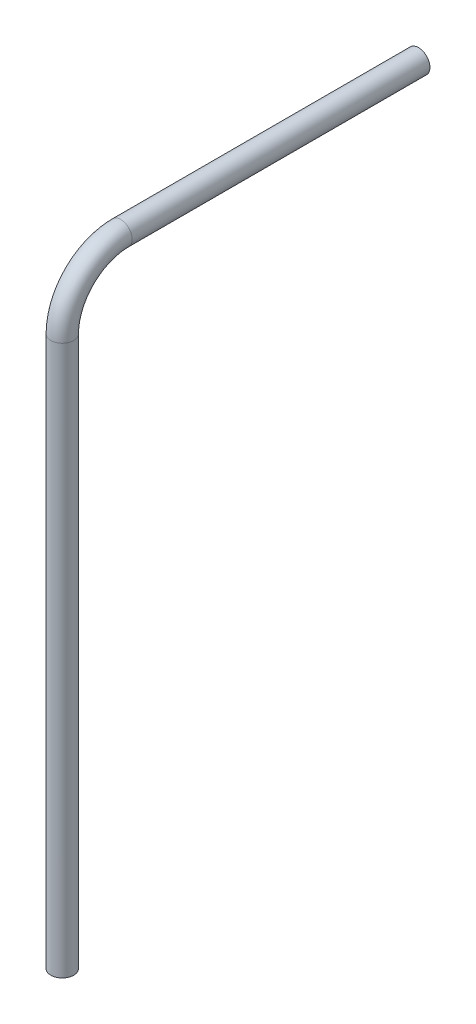
SolidWorks part; units mm, degrees
material "Cast Carbon Steel"
ref_plane "Front Plane" through (0, 0, 0) normal (0, 0, 1) x (1, 0, 0)
ref_plane "Top Plane" through (0, 0, 0) normal (0, 1, 0) x (1, 0, 0)
ref_plane "Right Plane" through (0, 0, 0) normal (1, 0, 0) x (0, 0, -1)
sketch "Sketch2" plane through (0, 0, 0) normal (1, 0, 0) x (0, 0, -1)
  arc A0 (-64.8338, 0) -> (0, 64.8338) centre (0, 0) cw
sketch "Sketch3" plane through (0, 0, 0) normal (0, 1, 0) x (1, 0, 0)
  circle A0 centre (0, -64.8338) radius 12.7
  circle A1 centre (0, -64.8338) radius 4.7625
  dimension "D1" = 25.4
  dimension "D2" = 7.9375
sweep "Sweep1" add profiles "Sketch3" path "Sketch2"
ref_plane "Plane1" through (0, 0, 0) normal (0, -1, 0) x (-1, 0, 0)
ref_plane "Plane2" through (0, 0, 0) normal (0, 0, -1) x (-1, 0, 0)
sketch "Sketch4" plane through (0, 0, 0) normal (0, -1, 0) x (-1, 0, 0)
  circle A0 centre (0, -64.8338) radius 12.7
  circle A1 centre (0, -64.8338) radius 4.7625
  dimension "D1" = 7.9375
  dimension "D2" = 25.4
extrude "Boss-Extrude3" add sketch "Sketch4" along normal blind 609.6
sketch "Sketch5" plane through (0, 0, 0) normal (0, 0, -1) x (-1, 0, 0)
  circle A2 centre (0, 64.8338) radius 4.7625
  circle A3 centre (0, 64.8338) radius 12.7
  circle A5 centre (0, 64.8338) radius 12.7 construction
  dimension "D2" = 25.4
extrude "Boss-Extrude4" add sketch "Sketch5" along normal blind 330.2
ref_plane "Plane3" through (-12.7, 0, 0) normal (-1, 0, 0) x (0, 0, 1)
sketch "Sketch6" plane through (-12.7, 0, 0) normal (-1, 0, 0) x (0, 0, 1)
  line L0 (52.1338, 0) -> (77.5338, 0) construction
  line L1 (57.15, -609.6) -> (69.85, -609.6)
  line L2 (57.15, -609.6) -> (57.15, 0)
  line L3 (57.15, 0) -> (69.85, 0)
  line L4 (69.85, -609.6) -> (69.85, 0)
  point P12 (63.5, -609.6)
  point P13 (63.5, -609.6)
  dimension "D1" = 57.15
  dimension "D2" = 63.5
  dimension "D3" = 609.6
extrude "Cut-Extrude1" cut sketch "Sketch6" against normal blind 6.35
